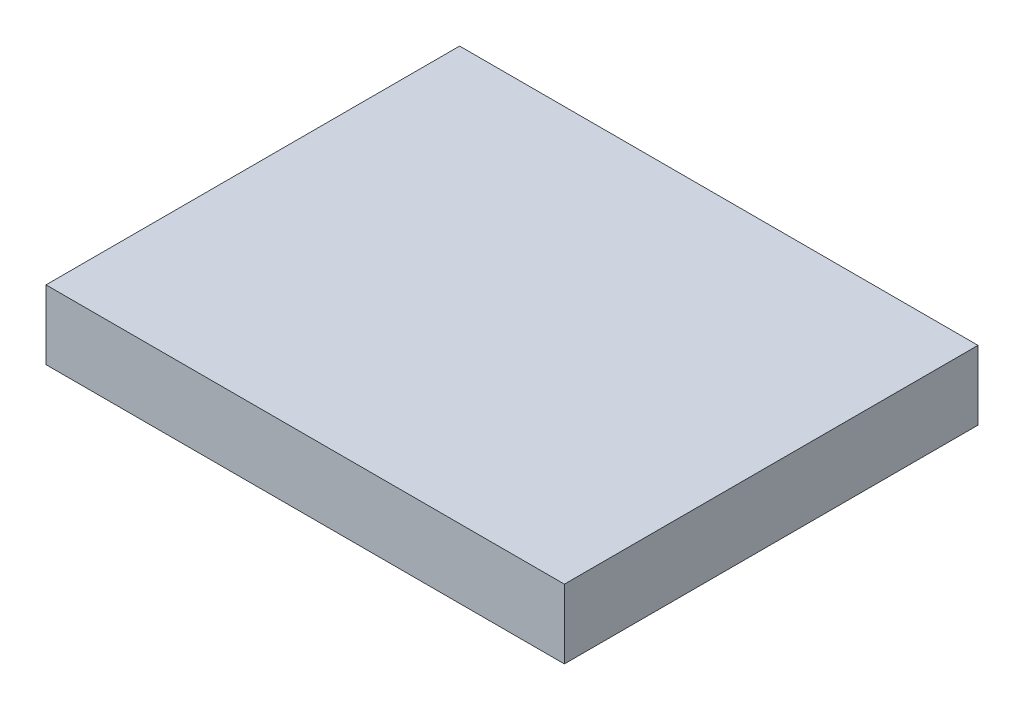
SolidWorks part; units mm, degrees
ref_plane "Front Plane" through (0, 0, 0) normal (0, 0, 1) x (1, 0, 0)
ref_plane "Top Plane" through (0, 0, 0) normal (0, 1, 0) x (1, 0, 0)
ref_plane "Right Plane" through (0, 0, 0) normal (1, 0, 0) x (0, 0, -1)
sketch "Sketch1" plane through (0, 0, 0) normal (0, 1, 0) x (1, 0, 0)
  line L1 (0, 0) -> (47.625, 0)
  line L2 (0, 0) -> (0, 38)
  line L3 (0, 38) -> (47.625, 38)
  line L4 (47.625, 0) -> (47.625, 38)
  dimension "D1" = 47.625
  dimension "D2" = 38
extrude "Boss-Extrude1" add sketch "Sketch1" along normal blind 6.35
